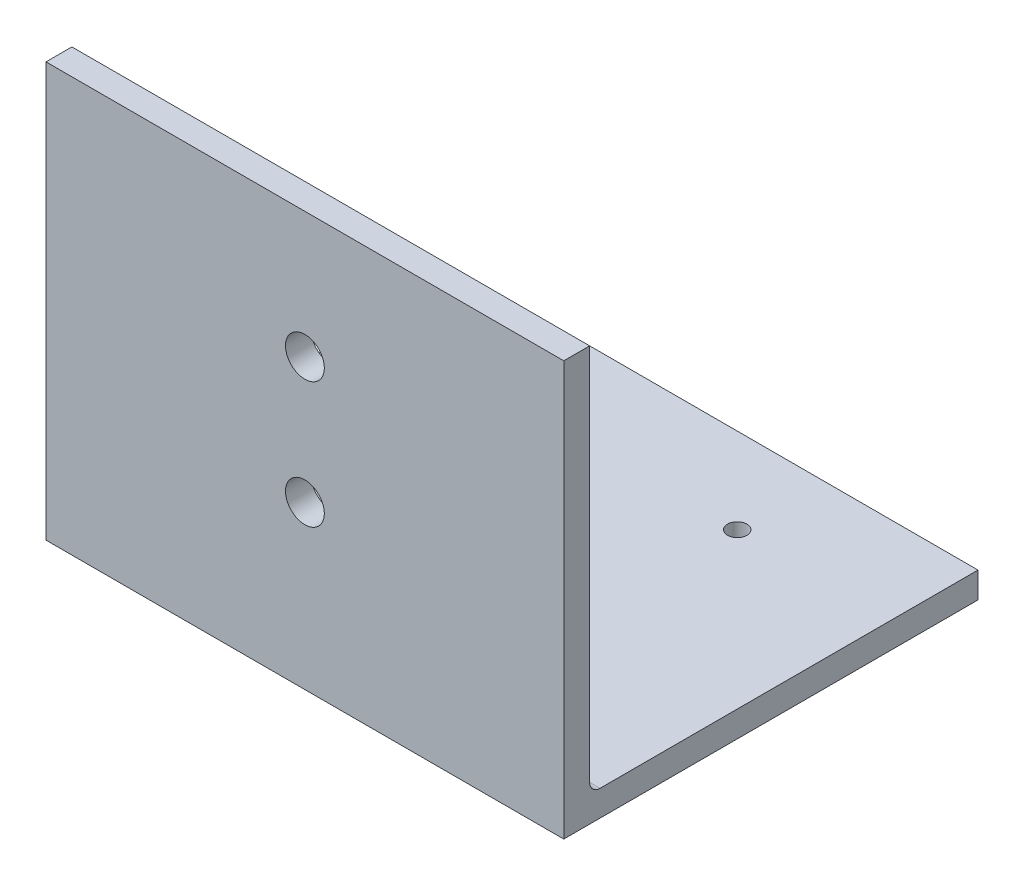
SolidWorks part; units mm, degrees
ref_plane "Front Plane" through (0, 0, 0) normal (0, 0, 1) x (1, 0, 0)
ref_plane "Top Plane" through (0, 0, 0) normal (0, 1, 0) x (1, 0, 0)
ref_plane "Right Plane" through (0, 0, 0) normal (1, 0, 0) x (0, 0, -1)
sketch "Sketch1" plane through (0, 0, 0) normal (1, 0, 0) x (0, 0, -1)
  line L0 (0, 0) -> (0, 101.6)
  line L9 (0, 101.6) -> (6.35, 101.6)
  line L10 (6.35, 101.6) -> (6.35, 6.35)
  line L11 (6.35, 6.35) -> (101.6, 6.35)
  line L12 (101.6, 6.35) -> (101.6, 0)
  line L13 (101.6, 0) -> (0, 0)
  dimension "D1" = 6.35
  dimension "D2" = 101.6
extrude "Boss-Extrude1" add sketch "Sketch1" along normal blind 127
fillet "Fillet1" radius 2.54 1 edges at (63.5, 6.35, -6.35)
sketch "Sketch2" plane through (0, 0, -6.35) normal (0, 0, -1) x (-1, 0, 0)
  line L0 (-127, 101.6) -> (0, 101.6) construction
  circle A0 centre (-63.5, 70.6967) radius 4.7625
  circle A1 centre (-63.5, 39.7933) radius 4.7625
  point P6 (-62.62, 41.8645)
  point P7 (-63.5, 101.6)
  dimension "D3" = 9.525
  dimension "D1" = 30.9033
  dimension "D2" = 30.9033
extrude "Cut-Extrude1" cut sketch "Sketch2" against normal up to surface (6.35 mm away) up to face at (63.5, 50.8, 0)
sketch "Sketch3" plane through (0, 6.35, 0) normal (0, 1, 0) x (1, 0, 0)
  line L0 (0, 101.6) -> (0, 8.89) construction
  line L2 (38.1, 80.645) -> (38.1, 29.845) construction
  circle A0 centre (38.1, 80.645) radius 2.3812
  circle A1 centre (88.9, 80.645) radius 2.3813
  circle A2 centre (38.1, 29.845) radius 2.3812
  circle A3 centre (88.9, 29.845) radius 2.3813
  point P8 (38.1, 55.245)
  point P9 (0, 55.245)
  dimension "D4" = 4.7625
  dimension "D1" = 50.8
  dimension "D2" = 50.8
  dimension "D3" = 38.1
extrude "Cut-Extrude2" cut sketch "Sketch3" against normal up to surface (6.35 mm away) up to face at (63.5, 0, -50.8)
